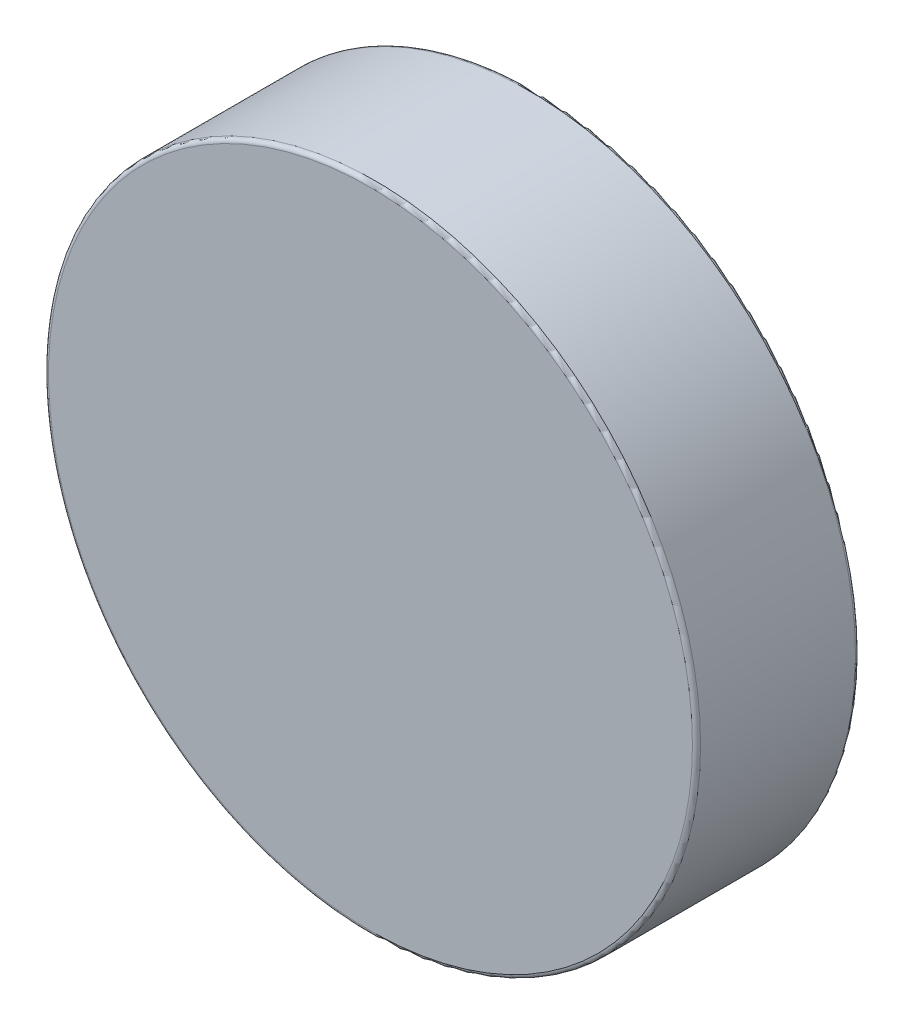
SolidWorks part; units mm, degrees
material "Nickel"
ref_plane "Front" through (0, 0, 0) normal (0, 0, 1) x (1, 0, 0)
ref_plane "Top" through (0, 0, 0) normal (0, 1, 0) x (1, 0, 0)
ref_plane "Right" through (0, 0, 0) normal (1, 0, 0) x (0, 0, -1)
sketch "Sketch1" plane through (0, 0, 0) normal (0, 0, 1) x (1, 0, 0)
  circle A0 centre (0, 0) radius 3.175 construction
  dimension "OD" = 6.35
sketch "Sketch2" plane through (0, 0, 0) normal (1, 0, 0) x (0, 0, -1)
  line L0 (-0.7937, 0) -> (0.7938, 0) construction
  line L1 (0, 3.175) -> (0, -3.175) construction
  line L3 (-0.7938, 3.175) -> (0.7937, 3.175)
  line L4 (-0.7938, 3.175) -> (-0.7938, -3.175)
  line L5 (-0.7938, -3.175) -> (0.7937, -3.175)
  line L6 (0.7937, 3.175) -> (0.7937, -3.175)
  point P4 (0, 0)
  point P12 (0, 3.175)
  dimension "Thickness" = 1.5875
sketch "Sketch3" plane through (0, 0, 0) normal (0, 0, 1) x (1, 0, 0)
  circle A0 centre (0, 0) radius 3.175 construction
  circle A1 centre (0, 0) radius 3.175
extrude "Boss-Extrude1" add sketch "Sketch3" along normal up to vertex (0.7937 mm away) and the other way up to vertex (0.7937 mm away) up to point (0, 3.175, 0.7938) other way up to point (0, 3.175, -0.7937)
fillet "Fillet1" radius 0.0397 2 edges at (3.175, 0, -0.7937) (3.175, 0, 0.7938)
